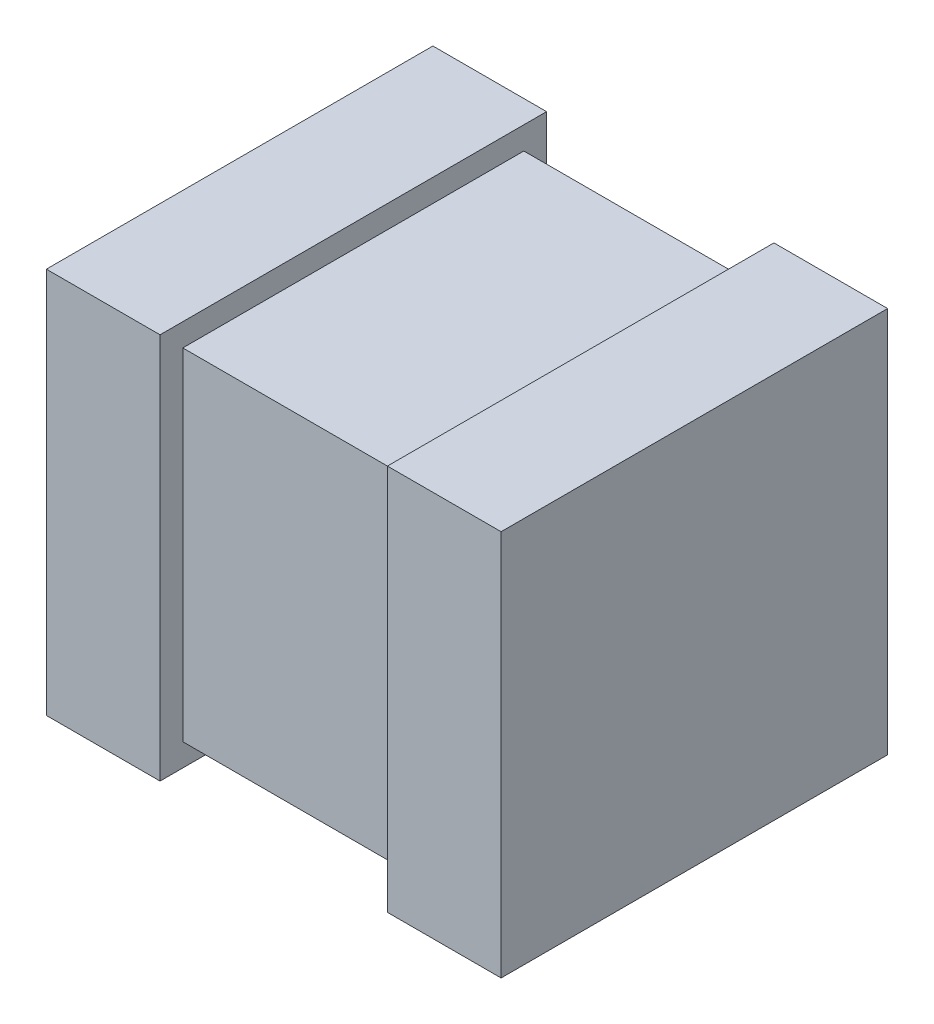
SolidWorks part; units mm, degrees
ref_plane "Front Plane" through (0, 0, 0) normal (0, 0, 1) x (1, 0, 0)
ref_plane "Top Plane" through (0, 0, 0) normal (0, 1, 0) x (1, 0, 0)
ref_plane "Right Plane" through (0, 0, 0) normal (1, 0, 0) x (0, 0, -1)
sketch "Chip" plane through (0, 0, 0) normal (0, 0, 1) x (1, 0, 0)
  line L0 (-0.508, -0.381) -> (0.508, -0.381)
  line L1 (-0.508, -0.381) -> (-0.508, 0.381)
  line L2 (0.508, 0.381) -> (-0.508, 0.381)
  line L3 (0.508, 0.381) -> (0.508, -0.381)
  dimension "D1" = 0.508
  dimension "D2" = 0.381
  dimension "W" = 0.762
  dimension "L" = 1.016
extrude "Chip Cap " add sketch "Chip" along normal blind 0.762
sketch "Solder Band" plane through (0.508, 0, 0) normal (1, 0, 0) x (0, 0, -1)
  line L0 (-0.8128, -0.4318) -> (0.0508, -0.4318)
  line L1 (-0.8128, -0.4318) -> (-0.8128, 0.4318)
  line L2 (0.0508, 0.4318) -> (-0.8128, 0.4318)
  line L3 (0.0508, 0.4318) -> (0.0508, -0.4318)
  line L4 (-0.762, 0.381) -> (-0.762, -0.381) construction
  line L5 (-0.762, -0.381) -> (0, -0.381) construction
  line L6 (0, 0.381) -> (0, -0.381) construction
  line L7 (-0.762, 0.381) -> (0, 0.381) construction
  dimension "D1" = 0.0508
  dimension "D2" = 0.0508
  dimension "D3" = 0.0508
  dimension "Solder" = 0.0508
extrude "Solder Band R" add sketch "Solder Band" against normal blind 0.254
sketch "Sketch3" plane through (-0.508, 0, 0) normal (-1, 0, 0) x (0, 0, 1)
  line L0 (-0.0508, 0.4318) -> (0.8128, 0.4318)
  line L1 (-0.0508, 0.4318) -> (-0.0508, -0.4318)
  line L2 (0.8128, -0.4318) -> (-0.0508, -0.4318)
  line L3 (0.8128, -0.4318) -> (0.8128, 0.4318)
extrude "Solder Band L" add sketch "Sketch3" against normal blind 0.254
ref_plane "Board Plane" through (0, -0.4318, 0) normal (0, 1, 0) x (-1, 0, 0)
sketch "Component_Outline" plane through (0, -0.4318, 0) normal (0, 1, 0) x (-1, 0, 0)
  line L1 (0.508, 0.8128) -> (-0.508, 0.8128)
  line L2 (0.508, 0.8128) -> (0.508, -0.0508)
  line L3 (0.508, -0.0508) -> (-0.508, -0.0508)
  line L4 (-0.508, 0.8128) -> (-0.508, -0.0508)
equation "\"D2@Chip\"=.5*\"W@Chip\""
equation "\"D1@Chip\"=.5*\"L@Chip\""
equation "\"D3@Solder Band\" = \"Solder@Solder Band\""
equation "\"D1@Solder Band\"=\"Solder@Solder Band\""
equation "\"D2@Solder Band\"=\"Solder@Solder Band\""
equation "\"D1@Solder Band L\"=\"MB@Solder Band R\""
